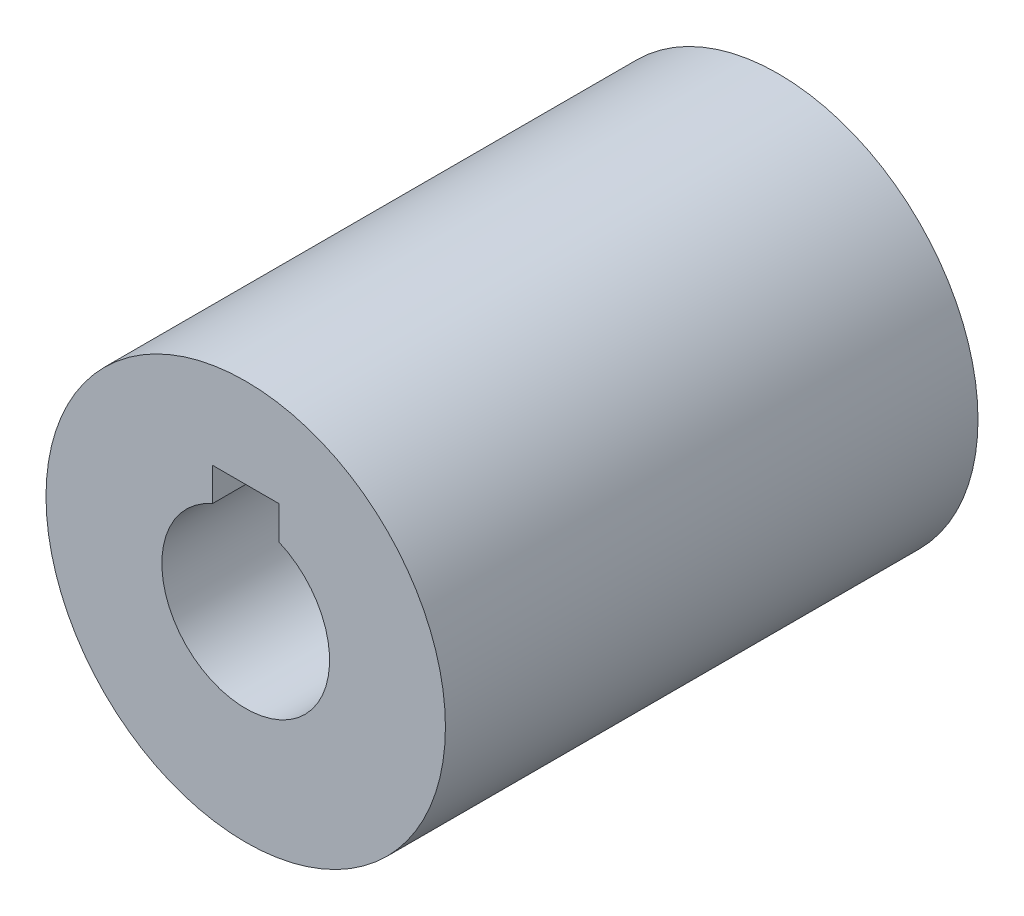
SolidWorks part; units mm, degrees
ref_plane "Front Plane" through (0, 0, 0) normal (0, 0, 1) x (1, 0, 0)
ref_plane "Top Plane" through (0, 0, 0) normal (0, 1, 0) x (1, 0, 0)
ref_plane "Right Plane" through (0, 0, 0) normal (1, 0, 0) x (0, 0, -1)
sketch "Sketch1" plane through (0, 0, 0) normal (0, 0, 1) x (1, 0, 0)
  circle A0 centre (0, 0) radius 9.525
  circle A1 centre (0, 0) radius 4
  dimension "D1" = 8
  dimension "D2" = 19.05
extrude "Boss-Extrude1" add sketch "Sketch1" along normal blind 25.4
sketch "Sketch2" plane through (0, 0, 25.4) normal (0, 0, 1) x (1, 0, 0)
  line L1 (-1.5875, 5.259) -> (1.5875, 5.259)
  line L2 (-1.5875, 5.259) -> (-1.5875, 3.6715)
  line L3 (-1.5875, 3.6715) -> (1.5875, 3.6715)
  line L4 (1.5875, 5.259) -> (1.5875, 3.6715)
  circle A0 centre (0, 0) radius 4 construction
  point P4 (0, 3.6715)
  point P6 (0, 0)
  point P9 (-2.9377, 2.7148)
  dimension "D1" = 1.5875
  dimension "D2" = 3.175
extrude "Cut-Extrude1" cut sketch "Sketch2" against normal through all
